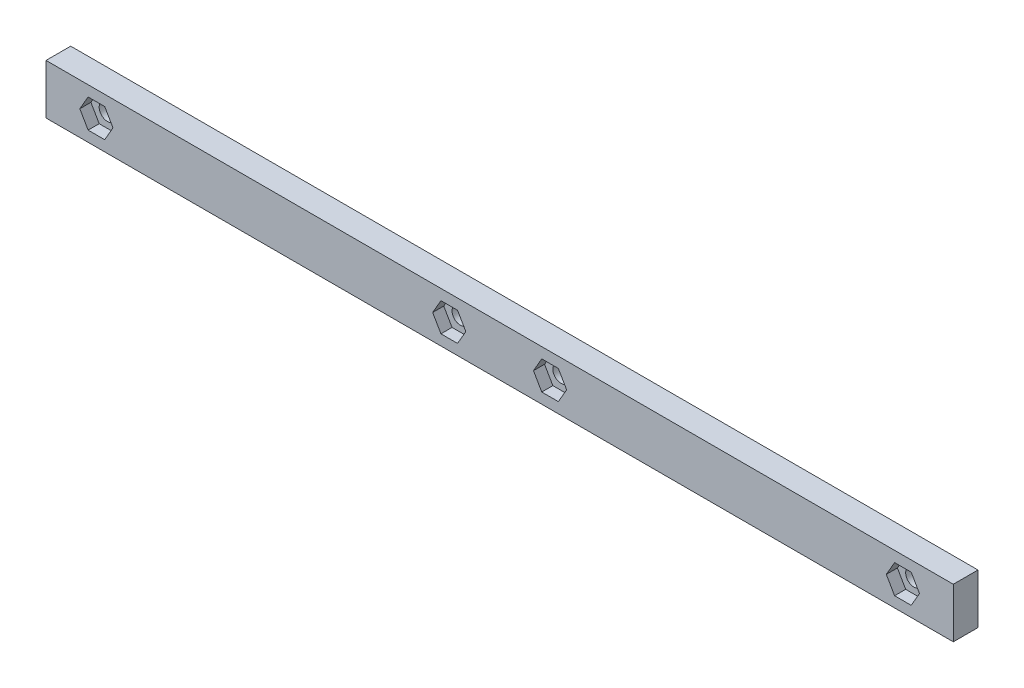
SolidWorks part; units mm, degrees
material "ABS"
ref_plane "Front Plane" through (0, 0, 0) normal (0, 0, 1) x (1, 0, 0)
ref_plane "Top Plane" through (0, 0, 0) normal (0, 1, 0) x (1, 0, 0)
ref_plane "Right Plane" through (0, 0, 0) normal (1, 0, 0) x (0, 0, -1)
sketch "Sketch1" plane through (0, 0, 0) normal (0, 0, 1) x (1, 0, 0)
  line L0 (-966.3573, 33.4408) -> (49033.6427, 33.4408) construction
  line L1 (-146.3573, 38.3908) -> (33.6427, 38.3908)
  line L2 (-146.3573, 38.3908) -> (-146.3573, 28.4908)
  line L3 (-146.3573, 28.4908) -> (33.6427, 28.4908)
  line L4 (33.6427, 38.3908) -> (33.6427, 28.4908)
  line L5 (33.6427, 38.4408) -> (33.6427, 28.4408) construction
  line L6 (-146.3573, 38.4408) -> (-146.3573, 28.4408) construction
  point P11 (33.6427, 33.4408)
  dimension "D1" = 9.9
extrude "Boss-Extrude1" add sketch "Sketch1" against normal blind 4.9
sketch "Sketch2" plane through (0, 0, 0) normal (0, 0, 1) x (1, 0, 0)
  circle A0 centre (-136.3573, 33.4408) radius 1.65
  circle A1 centre (-66.3573, 33.4408) radius 1.65
  circle A2 centre (-46.3573, 33.4408) radius 1.65
  circle A3 centre (23.6427, 33.4408) radius 1.65
  circle A4 centre (-136.3573, 33.4408) radius 1.65 construction
extrude "Cut-Extrude1" cut sketch "Sketch2" against normal through all
sketch "Sketch3" plane through (0, 0, 0) normal (0, 0, 1) x (1, 0, 0)
  line L1 (-134.7119, 30.5908) -> (-133.0665, 33.4408)
  line L2 (-133.0665, 33.4408) -> (-134.7119, 36.2908)
  line L3 (-134.7119, 36.2908) -> (-138.0028, 36.2908)
  line L4 (-138.0028, 36.2908) -> (-139.6482, 33.4408)
  line L5 (-139.6482, 33.4408) -> (-138.0028, 30.5908)
  line L6 (-138.0028, 30.5908) -> (-134.7119, 30.5908)
  line L7 (-64.7119, 30.5908) -> (-63.0665, 33.4408)
  line L8 (-63.0665, 33.4408) -> (-64.7119, 36.2908)
  line L9 (-64.7119, 36.2908) -> (-68.0028, 36.2908)
  line L10 (-68.0028, 36.2908) -> (-69.6482, 33.4408)
  line L11 (-69.6482, 33.4408) -> (-68.0028, 30.5908)
  line L12 (-68.0028, 30.5908) -> (-64.7119, 30.5908)
  line L13 (-44.7119, 30.5908) -> (-43.0665, 33.4408)
  line L14 (-43.0665, 33.4408) -> (-44.7119, 36.2908)
  line L15 (-44.7119, 36.2908) -> (-48.0028, 36.2908)
  line L16 (-48.0028, 36.2908) -> (-49.6482, 33.4408)
  line L17 (-49.6482, 33.4408) -> (-48.0028, 30.5908)
  line L18 (-48.0028, 30.5908) -> (-44.7119, 30.5908)
  line L19 (25.2881, 30.5908) -> (26.9335, 33.4408)
  line L20 (26.9335, 33.4408) -> (25.2881, 36.2908)
  line L21 (25.2881, 36.2908) -> (21.9972, 36.2908)
  line L22 (21.9972, 36.2908) -> (20.3518, 33.4408)
  line L23 (20.3518, 33.4408) -> (21.9972, 30.5908)
  line L24 (21.9972, 30.5908) -> (25.2881, 30.5908)
  circle A0 centre (-136.3573, 33.4408) radius 2.85 construction
  circle A1 centre (-66.3573, 33.4408) radius 2.85 construction
  circle A2 centre (-46.3573, 33.4408) radius 2.85 construction
  circle A3 centre (23.6427, 33.4408) radius 2.85 construction
  dimension "D1" = 5.7
extrude "Cut-Extrude2" cut sketch "Sketch3" against normal blind 2.2
